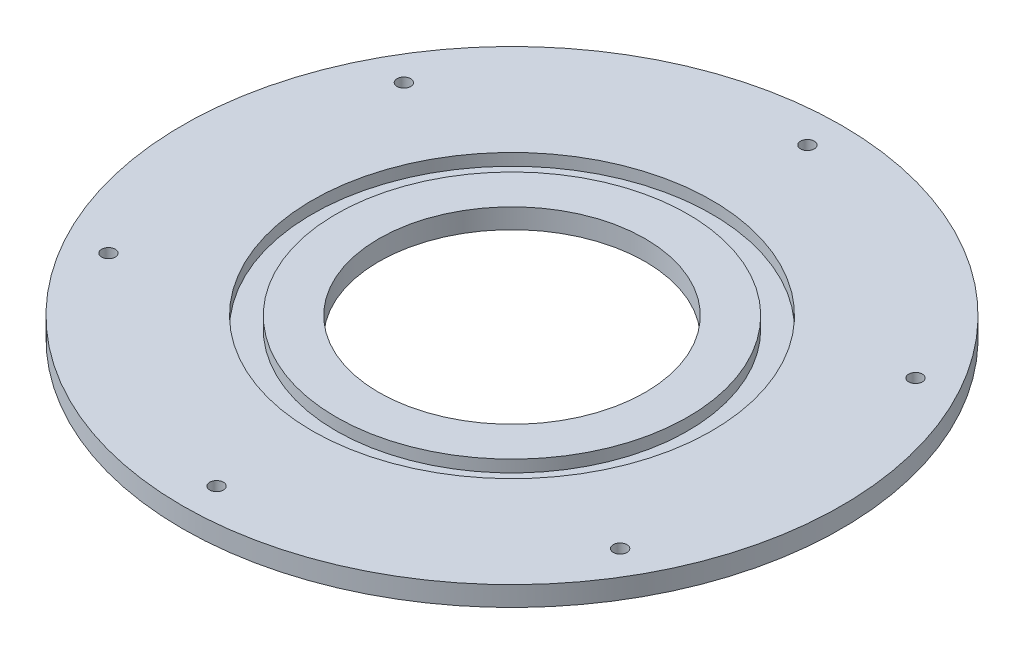
SolidWorks part; units mm, degrees
ref_plane "Front Plane" through (0, 0, 0) normal (0, 0, 1) x (1, 0, 0)
ref_plane "Top Plane" through (0, 0, 0) normal (0, 1, 0) x (1, 0, 0)
ref_plane "Right Plane" through (0, 0, 0) normal (1, 0, 0) x (0, 0, -1)
sketch "Sketch1" plane through (0, 0, 0) normal (0, 1, 0) x (1, 0, 0)
  circle A0 centre (0, 0) radius 96.5
  circle A1 centre (0, 0) radius 39
  dimension "D1" = 193
  dimension "D2" = 78
extrude "Boss-Extrude1" add sketch "Sketch1" along normal blind 5.8
sketch "Sketch2" plane through (0, 5.8, 0) normal (0, 1, 0) x (1, 0, 0)
  circle A0 centre (0, 0) radius 51.5
  circle A1 centre (0, 0) radius 58.5
  dimension "D1" = 103
  dimension "D2" = 117
extrude "Cut-Extrude1" cut sketch "Sketch2" against normal blind 3.5
sketch "Sketch3" plane through (0, 5.8, 0) normal (0, 1, 0) x (1, 0, 0)
  circle A0 centre (0, 0) radius 86.5 construction
  circle A1 centre (0, 86.5) radius 2
  circle A2 centre (74.9112, 43.25) radius 2
  circle A3 centre (74.9112, -43.25) radius 2
  circle A4 centre (0, -86.5) radius 2
  circle A5 centre (-74.9112, -43.25) radius 2
  circle A6 centre (-74.9112, 43.25) radius 2
  point P17 (0, 0)
  dimension "D1" = 173
  dimension "D2" = 4
  dimension "D3" = 6
extrude "Cut-Extrude2" cut sketch "Sketch3" against normal through all
